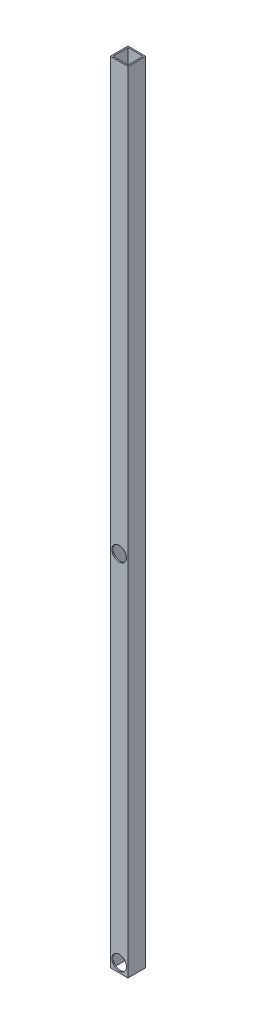
SolidWorks part; units mm, degrees
material "6063-T6"
ref_plane "Front Plane" through (0, 0, 0) normal (0, 0, 1) x (1, 0, 0)
ref_plane "Top Plane" through (0, 0, 0) normal (0, 1, 0) x (1, 0, 0)
ref_plane "Right Plane" through (0, 0, 0) normal (1, 0, 0) x (0, 0, -1)
sketch "Sketch1" plane through (0, 0, 0) normal (0, 1, 0) x (1, 0, 0)
  line L0 (41.275, 3.175) -> (41.275, 41.275)
  line L1 (0, 0) -> (44.45, 0)
  line L2 (0, 0) -> (0, 44.45)
  line L3 (0, 44.45) -> (44.45, 44.45)
  line L4 (44.45, 0) -> (44.45, 44.45)
  line L5 (3.175, 41.275) -> (41.275, 41.275)
  line L6 (3.175, 3.175) -> (3.175, 41.275)
  line L7 (3.175, 3.175) -> (41.275, 3.175)
  dimension "D1" = 44.45
  dimension "D2" = 3.175
extrude "Boss-Extrude1" add sketch "Sketch1" along normal blind 1981.2
sketch "Sketch2" plane through (0, 0, 0) normal (0, 0, 1) x (1, 0, 0)
  line L0 (0, 0) -> (44.45, 0) construction
  line L1 (44.45, 1981.2) -> (44.45, 0) construction
  circle A0 centre (22.225, 22.225) radius 18.2562
  circle A1 centre (22.225, 911.225) radius 18.2563
  dimension "D1" = 889
  dimension "D4" = 36.5125
  dimension "D2" = 22.225
  dimension "D3" = 22.225
extrude "Cut-Extrude1" cut sketch "Sketch2" against normal up to next
sketch "Sketch3" plane through (44.45, 0, 0) normal (1, 0, 0) x (0, 0, -1)
  line L0 (44.45, 1981.2) -> (44.45, 0) construction
  line L1 (0, 0) -> (44.45, 0) construction
  circle A0 centre (22.225, 22.225) radius 4.7625
  circle A1 centre (22.225, 911.225) radius 4.7625
  dimension "D1" = 889
  dimension "D4" = 9.525
  dimension "D2" = 22.225
  dimension "D3" = 22.225
sketch "Sketch4" plane through (0, 0, -44.45) normal (0, 0, -1) x (-1, 0, 0)
  circle A0 centre (-22.225, 911.225) radius 12.7
  circle A1 centre (-22.225, 22.225) radius 12.7
  dimension "D1" = 25.4
extrude "Cut-Extrude2" cut sketch "Sketch4" against normal up to next
